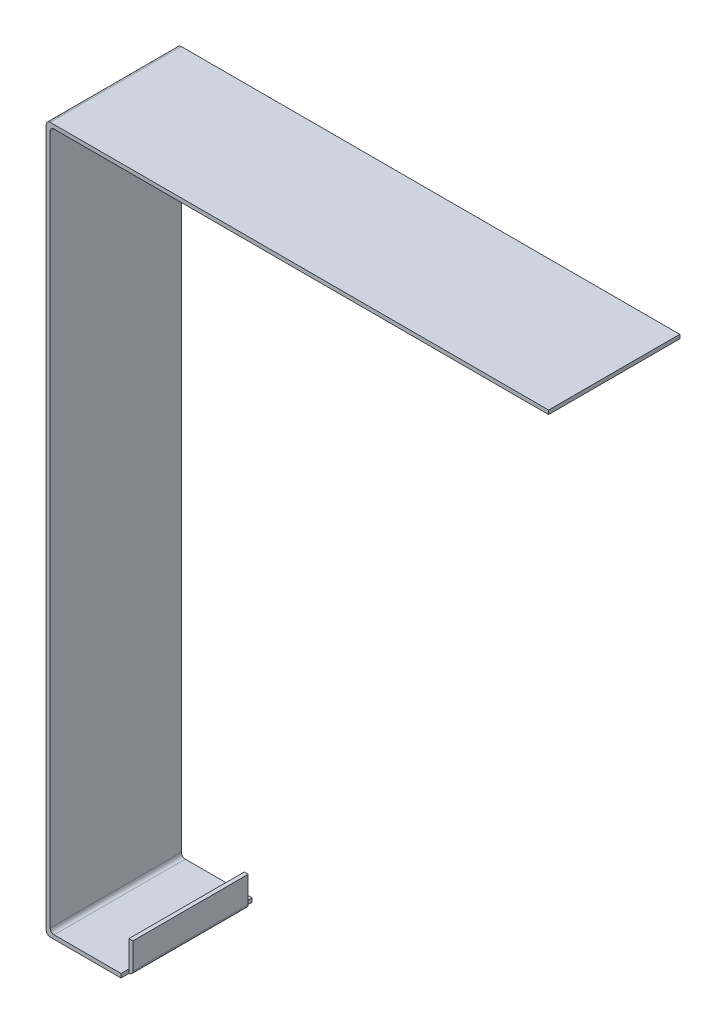
SolidWorks part; units mm, degrees
ref_plane "前视基准面" through (0, 0, 0) normal (0, 0, 1) x (1, 0, 0)
ref_plane "上视基准面" through (0, 0, 0) normal (0, 1, 0) x (1, 0, 0)
ref_plane "右视基准面" through (0, 0, 0) normal (1, 0, 0) x (0, 0, -1)
sketch "草图1" plane through (0, 0, 0) normal (0, 0, 1) x (1, 0, 0)
  line L0 (-40.5827, 29.8611) -> (147.9173, 29.8611)
  line L1 (147.9173, 29.8611) -> (147.9173, 31.3611)
  line L2 (-42.0827, 28.3611) -> (-42.0827, -50.1389)
  line L3 (-42.0827, -50.1389) -> (-42.0827, -226.1389)
  line L4 (-42.0827, -226.1389) -> (-42.0827, -234.6389)
  line L5 (-40.5827, -236.1389) -> (-16.5827, -236.1389)
  line L6 (-15.0827, -234.6389) -> (-15.0827, -226.1389)
  line L7 (-15.0827, -226.1389) -> (-13.5827, -226.1389)
  line L8 (-13.5827, -226.1389) -> (-13.5827, -236.1389)
  line L9 (-15.0827, -237.6389) -> (-42.0827, -237.6389)
  line L10 (-43.5827, -236.1389) -> (-43.5827, 29.8611)
  line L12 (-42.0827, 31.3611) -> (147.9173, 31.3611)
  line L13 (-13.5827, -236.1389) -> (-13.5827, -237.6389)
  line L14 (-13.5827, -237.6389) -> (-15.0827, -237.6389)
  line L15 (-15.0827, -234.6389) -> (-15.0827, -236.1389)
  line L16 (-15.0827, -236.1389) -> (-16.5827, -236.1389)
  arc A2 (-43.5827, -236.1389) -> (-42.0827, -237.6389) centre (-42.0827, -236.1389) ccw
  arc A3 (-42.0827, -234.6389) -> (-40.5827, -236.1389) centre (-40.5827, -234.6389) ccw
  arc A4 (-42.0827, 28.3611) -> (-40.5827, 29.8611) centre (-40.5827, 28.3611) cw
  arc A5 (-43.5827, 29.8611) -> (-42.0827, 31.3611) centre (-42.0827, 29.8611) cw
  dimension "D1" = 1.5
extrude "凸台-拉伸1" add sketch "草图1" along normal blind 50
sketch "草图3" plane through (-13.5827, 0, 0) normal (1, 0, 0) x (0, 0, -1)
  line L0 (-50, -237.6389) -> (-47, -237.6389)
  line L1 (-50, -237.6389) -> (0, -237.6389) construction
  line L2 (-47, -237.6389) -> (-47, -226.1389)
  line L3 (-50, -226.1389) -> (0, -226.1389) construction
  line L4 (-47, -226.1389) -> (-50, -226.1389)
  line L5 (-50, -226.1389) -> (-50, -237.6389)
  line L6 (-25, -237.6389) -> (-25, -199.0232) construction
  line L7 (0, -226.1389) -> (0, -237.6389)
  line L8 (-3, -226.1389) -> (0, -226.1389)
  line L9 (-3, -237.6389) -> (-3, -226.1389)
  line L10 (0, -237.6389) -> (-3, -237.6389)
extrude "切除-拉伸1" cut sketch "草图3" against normal blind 1.5
fillet "圆角1" radius 1.5 3 edges at (-13.5827, -237.6389, 25) (-14.3327, -237.6389, 47) (-14.3327, -237.6389, 3)
